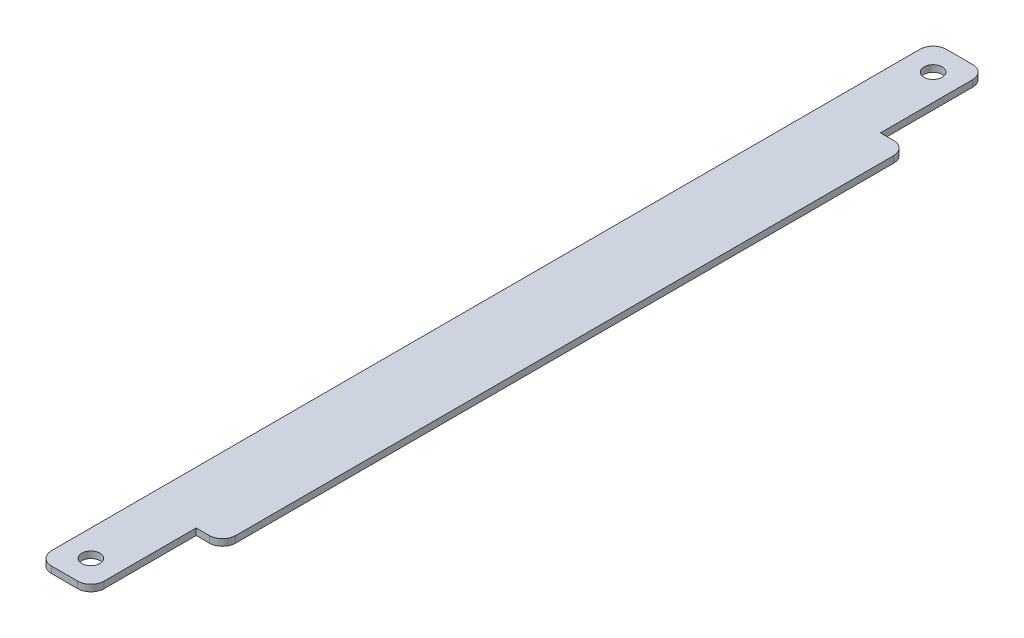
SolidWorks part; units mm, degrees
ref_plane "Front Plane" through (0, 0, 0) normal (0, 0, 1) x (1, 0, 0)
ref_plane "Top Plane" through (0, 0, 0) normal (0, 1, 0) x (1, 0, 0)
ref_plane "Right Plane" through (0, 0, 0) normal (1, 0, 0) x (0, 0, -1)
sketch "Sketch1" plane through (0, 0, 0) normal (0, 1, 0) x (1, 0, 0)
  line L0 (0, 3.175) -> (0, 212.725)
  line L1 (3.175, 215.9) -> (9.525, 215.9)
  line L2 (12.7, 212.725) -> (12.7, 190.5)
  line L3 (12.7, 190.5) -> (15.875, 190.5)
  line L4 (19.05, 187.325) -> (19.05, 28.575)
  line L5 (15.875, 25.4) -> (12.7, 25.4)
  line L6 (12.7, 25.4) -> (12.7, 3.175)
  line L7 (9.525, 0) -> (3.175, 0)
  circle A0 centre (6.35, 209.55) radius 2.1828
  circle A1 centre (6.35, 6.35) radius 2.1828
  arc A2 (0, 3.175) -> (3.175, 0) centre (3.175, 3.175) ccw
  arc A3 (9.525, 0) -> (12.7, 3.175) centre (9.525, 3.175) ccw
  arc A4 (15.875, 25.4) -> (19.05, 28.575) centre (15.875, 28.575) ccw
  arc A5 (19.05, 187.325) -> (15.875, 190.5) centre (15.875, 187.325) ccw
  arc A6 (12.7, 212.725) -> (9.525, 215.9) centre (9.525, 212.725) ccw
  arc A7 (3.175, 215.9) -> (0, 212.725) centre (3.175, 212.725) ccw
  point P7 (6.35, 215.9)
  point P16 (0, 0)
  point P19 (12.7, 0)
  point P22 (19.05, 25.4)
  point P29 (0, 215.9)
  dimension "D9" = 4.3656
  dimension "D12" = 4.3656
  dimension "D13" = 3.175
  dimension "D1" = 215.9
  dimension "D2" = 12.7
  dimension "D3" = 6.35
  dimension "D4" = 25.4
  dimension "D5" = 12.7
  dimension "D6" = 25.4
  dimension "D7" = 6.35
  dimension "D8" = 6.35
  dimension "D10" = 6.35
  dimension "D11" = 6.35
extrude "Boss-Extrude1" add sketch "Sketch1" along normal blind 1.5875
